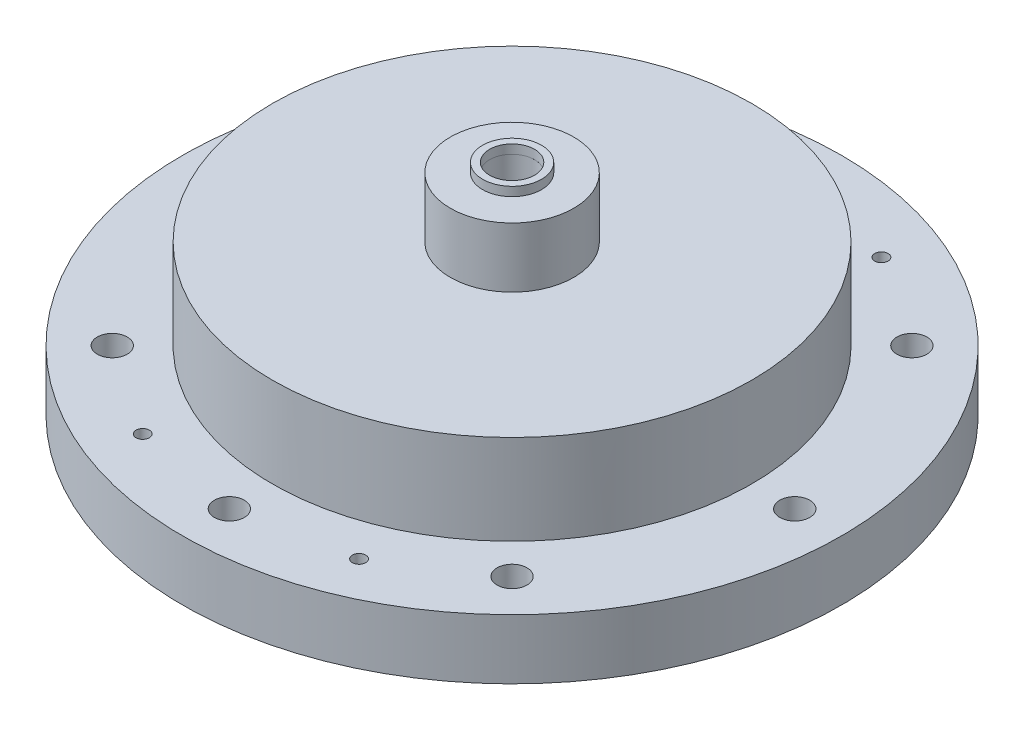
SolidWorks part; units mm, degrees
ref_plane "Front Plane" through (0, 0, 0) normal (0, 0, 1) x (1, 0, 0)
ref_plane "Top Plane" through (0, 0, 0) normal (0, 1, 0) x (1, 0, 0)
ref_plane "Right Plane" through (0, 0, 0) normal (1, 0, 0) x (0, 0, -1)
sketch "Sketch1" plane through (0, 0, 0) normal (0, 1, 0) x (1, 0, 0)
  circle A1 centre (0, 0) radius 50.8
  dimension "D1" = 101.6
extrude "Boss-Extrude1" add sketch "Sketch1" along normal blind 25.4
sketch "Sketch2" plane through (0, 0, 0) normal (0, -1, 0) x (1, 0, 0)
  circle A0 centre (0, 0) radius 50.8
  circle A1 centre (0, 0) radius 69.85
  dimension "D1" = 139.7
extrude "Boss-Extrude2" add sketch "Sketch2" against normal blind 12.7
sketch "Sketch4" plane through (0, 0, 0) normal (0, -1, 0) x (1, 0, 0)
  circle A0 centre (0, -59.9186) radius 3.175
  circle A1 centre (-42.3688, -42.3688) radius 3.175
  circle A2 centre (-59.9186, 0) radius 3.175
  circle A3 centre (-42.3688, 42.3688) radius 3.175
  circle A4 centre (0, 59.9186) radius 3.175
  circle A5 centre (42.3688, 42.3688) radius 3.175
  circle A6 centre (59.9186, 0) radius 3.175
  circle A7 centre (42.3688, -42.3688) radius 3.175
  point P35 (0, 0)
  dimension "D2" = 6.35
  dimension "D1" = 59.9186
  dimension "D3" = 8
extrude "Cut-Extrude2" cut sketch "Sketch4" against normal up to next
sketch "Sketch5" plane through (0, 25.4, 0) normal (0, 1, 0) x (1, 0, 0)
  circle A0 centre (0, 0) radius 12.827
  dimension "D1" = 25.654
extrude "Cut-Extrude3" cut sketch "Sketch5" against normal blind 19.05 from offset 0
sketch "Sketch6" plane through (0, 6.35, 0) normal (0, 1, 0) x (1, 0, 0)
  circle A0 centre (0, 0) radius 1.5875
  dimension "D1" = 3.175
extrude "Cut-Extrude4" cut sketch "Sketch6" against normal up to next
sketch "Sketch34" plane through (0, 25.4, 0) normal (0, 1, 0) x (1, 0, 0)
  circle A0 centre (0, 0) radius 13.081
  circle A1 centre (0, 0) radius 4.7625
  dimension "D1" = 26.162
  dimension "D2" = 9.525
extrude "Boss-Extrude3" add sketch "Sketch34" along normal blind 19.05
cosmetic thread "Cosmetic Thread4" parameters "D2"=23.1953
sketch "Sketch40" plane through (0, 25.4, 0) normal (0, 1, 0) x (1, 0, 0)
  circle A0 centre (0, 0) radius 50.8
extrude "Boss-Extrude5" add sketch "Sketch40" along normal blind 6.35
sketch "Sketch38" plane through (0, 44.45, 0) normal (0, 1, 0) x (1, 0, 0)
  circle A0 centre (0, 0) radius 6.2484
  dimension "D1" = 12.4968
extrude "Boss-Extrude4" add sketch "Sketch38" along normal blind 1.905 separate body
sketch "Sketch39" plane through (0, 46.355, 0) normal (0, 1, 0) x (1, 0, 0)
  circle A0 centre (0, 0) radius 4.7625
  dimension "D1" = 9.525
extrude "Cut-Extrude7" cut sketch "Sketch39" against normal blind 50.8
sketch "Sketch41" plane through (0, 31.75, 0) normal (0, 1, 0) x (1, 0, 0)
  circle A0 centre (0, 0) radius 4.7625
  dimension "D1" = 9.525
extrude "Cut-Extrude8" cut sketch "Sketch41" against normal blind 6.35
sketch "Sketch42" plane through (0, 0, 0) normal (0, -1, 0) x (1, 0, 0)
  circle A0 centre (0, 0) radius 23.7871
  dimension "D1" = 47.5742
extrude "Cut-Extrude9" [suppressed] cut sketch "Sketch42" against normal blind 6.477
hole_wizard "#10-24 Tapped Hole1" [suppressed] positions "Sketch44" profile "Sketch45" tap size "#10-24" standard "ANSI Inch"
sketch "Sketch44" [suppressed] plane through (0, 6.477, 0) normal (0, -1, 0) x (-1, 0, 0)
  line L0 (0, 0) -> (0, -35.56) construction
  line L2 (0, 0) -> (0, 30.48) construction
  line L4 (0, 0) -> (-27.94, 0) construction
  line L6 (0, 0) -> (30.48, 0) construction
  circle A0 centre (0, 0) radius 17.4625 construction
  point P0 (0, -17.4625)
  point P2 (-17.4625, 0)
  point P4 (0, 17.4625)
  point P6 (17.4625, 0)
  dimension "D1" = 34.925
sketch "Sketch45" plane through (0, 6.477, 17.4625) normal (1, 0, 0) x (0, 0, -1)
  line L0 (0, 0) -> (0, 13.8408)
  line L1 (0, 13.8408) -> (1.8986, 12.7)
  line L2 (1.8986, 12.7) -> (1.8986, 0)
  line L5 (1.8986, 0) -> (0, 0)
  line L10 (0, 13.8408) -> (-1.8987, 12.7) construction
  line L11 (0, -6.35) -> (0, 107.95) construction
  dimension "Tap Drill Dia." = 3.7973
  dimension "Tap Drill Depth" = 12.7
  dimension "Drill Angle" = 118
cosmetic thread "Hole Thread1" parameters "D1"=9.652, "D2"=4.826
cosmetic thread "Hole Thread2" parameters "D1"=9.652, "D2"=4.826
cosmetic thread "Hole Thread3" parameters "D1"=9.652, "D2"=4.826
cosmetic thread "Hole Thread4" parameters "D1"=9.652, "D2"=4.826
sketch "Sketch46" plane through (0, 0, 0) normal (0, -1, 0) x (1, 0, 0)
  line L0 (0, -83.82) -> (0, 83.82) construction
  line L1 (34.3522, -82.9336) -> (-34.3522, 82.9336) construction
  line L2 (-32.8909, -79.4057) -> (32.8909, 79.4057) construction
  circle A0 centre (0, 0) radius 59.9186 construction
  circle A1 centre (-22.9299, 55.3576) radius 3.175
  circle A2 centre (22.9299, 55.3576) radius 3.175
  circle A3 centre (-22.9299, -55.3576) radius 3.175
  circle A4 centre (22.9299, -55.3576) radius 3.175
  point P7 (0, 0)
  point P10 (0, 0)
  point P12 (0, 0)
  dimension "D1" = 119.8372
  dimension "D4" = 6.35
  dimension "D5" = 6.35
  dimension "D6" = 6.35
  dimension "D7" = 6.35
  dimension "D2" = 22.5
  dimension "D3" = 22.5
extrude "Cut-Extrude10" cut sketch "Sketch46" against normal blind 6.35
hole_wizard "1/4-20 Tapped Hole1" [suppressed] positions "Sketch47" profile "Sketch48" tap size "1/4-20" standard "ANSI Inch"
sketch "Sketch47" plane through (0, 31.75, 0) normal (0, 1, 0) x (1, 0, 0)
  line L0 (0, 0) -> (0, 45.3569) construction
  line L2 (0, 0) -> (-40.0078, -23.0985) construction
  line L4 (0, 0) -> (38.662, -22.3215) construction
  circle A0 centre (0, 0) radius 38.1 construction
  point P0 (0, 38.1)
  point P2 (32.9956, -19.05)
  point P4 (-32.9956, -19.05)
  dimension "D1" = 76.2
  dimension "D2" = 120
  dimension "D3" = 120
sketch "Sketch48" plane through (0, 31.75, -38.1) normal (1, 0, 0) x (0, 0, 1)
  line L0 (0, 0) -> (0, 15.5038)
  line L1 (0, 15.5038) -> (2.5527, 13.97)
  line L2 (2.5527, 13.97) -> (2.5527, 0)
  line L5 (2.5527, 0) -> (0, 0)
  line L10 (0, 15.5038) -> (-2.5527, 13.97) construction
  line L11 (0, -6.35) -> (0, 107.95) construction
  dimension "Tap Drill Dia." = 5.1054
  dimension "Tap Drill Depth" = 13.97
  dimension "Drill Angle" = 118
cosmetic thread "Hole Thread5" [suppressed] parameters "D1"=12.7, "D2"=6.35
cosmetic thread "Hole Thread6" [suppressed] parameters "D1"=12.7, "D2"=6.35
cosmetic thread "Hole Thread7" [suppressed] parameters "D1"=12.7, "D2"=6.35
sketch "Sketch49" [suppressed] plane through (0, 6.477, 0) normal (0, -1, 0) x (1, 0, 0)
  circle A0 centre (0, 0) radius 23.8252
  dimension "D1" = 47.6504
extrude "Cut-Extrude11" cut sketch "Sketch49" against normal blind 3.937 from surface at 6.477 starting at face at (22.9299, 0, 52.1826)
sketch "Sketch50" plane through (0, 6.35, 0) normal (0, -1, 0) x (1, 0, 0)
  circle A0 centre (-22.9299, 55.3576) radius 1.4097
  circle A1 centre (22.9299, 55.3576) radius 1.4097
  circle A2 centre (-22.9299, -55.3576) radius 1.4097
  circle A3 centre (22.9299, -55.3576) radius 1.4097
  dimension "D1" = 2.8194
  dimension "D2" = 2.8194
  dimension "D3" = 2.8194
  dimension "D4" = 2.8194
extrude "Cut-Extrude12" cut sketch "Sketch50" against normal through all
sketch "Sketch51" plane through (0, 0, 0) normal (0, -1, 0) x (1, 0, 0)
  circle A0 centre (0, 0) radius 44.45
extrude "Cut-Extrude13" cut sketch "Sketch51" against normal blind 25.4
sketch "Sketch52" plane through (0, 0, 0) normal (0, -1, 0) x (-1, 0, 0)
  circle A0 centre (0, 0) radius 4.7625
  circle A1 centre (0, 0) radius 44.45
  dimension "D1" = 9.525
extrude "Boss-Extrude6" add sketch "Sketch52" against normal blind 25.4
sketch "Sketch53" plane through (0, 0, 0) normal (0, -1, 0) x (1, 0, 0)
  circle A0 centre (0, 0) radius 44.45
  dimension "D1" = 88.9
extrude "Cut-Extrude14" cut sketch "Sketch53" against normal blind 25.4
